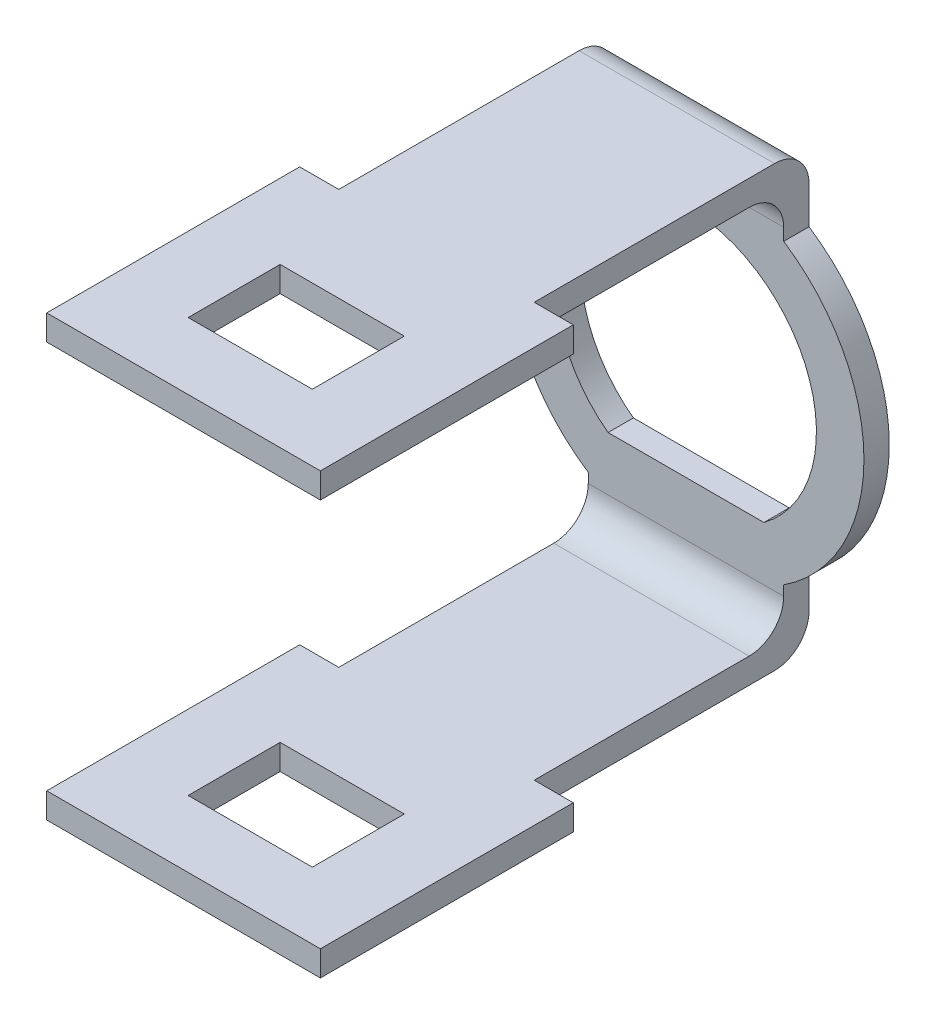
SolidWorks part; units mm, degrees
ref_plane "Front Plane" through (0, 0, 0) normal (0, 0, 1) x (1, 0, 0)
ref_plane "Top Plane" through (0, 0, 0) normal (0, 1, 0) x (1, 0, 0)
ref_plane "Right Plane" through (0, 0, 0) normal (1, 0, 0) x (0, 0, -1)
sketch "Sketch1" plane through (0, 0, 0) normal (0, 0, 1) x (1, 0, 0)
  line L0 (-3.3886, -4.5495) -> (3.3886, -4.5495)
  line L2 (3.952, -6.655) -> (-3.9716, -6.655)
  line L5 (4.25, 6.4687) -> (-4.25, 6.4807)
  arc A0 (3.3886, -4.5495) -> (-3.3886, -4.5495) centre (0, 0) ccw
  arc A2 (-4.25, 6.4807) -> (-3.9716, -6.655) centre (0, 0) ccw
  arc A3 (3.952, -6.655) -> (4.25, 6.4687) centre (0, 0) ccw
extrude "Boss-Extrude1" add sketch "Sketch1" along normal blind 1.1
ref_plane "Plane1" through (0, -8.4, 0) normal (0, -1, 0) x (-1, 0, 0)
sketch "Sketch3" plane through (0, -8.4, 0) normal (0, -1, 0) x (-1, 0, 0)
  line L0 (2.7, -20.05) -> (2.7, -16.05)
  line L1 (-5.95, -22.95) -> (5.95, -22.95)
  line L2 (-2.7, -20.05) -> (-2.7, -16.05)
  line L3 (2.55, -20.05) -> (-2.55, -20.05) construction
  line L4 (-5.95, -22.95) -> (-5.95, -11.95)
  line L5 (-5.95, -11.95) -> (5.95, -11.95)
  line L6 (5.95, -22.95) -> (5.95, -11.95)
  line L7 (-2.7, -16.05) -> (2.7, -16.05)
  line L8 (2.7, -20.05) -> (-2.7, -20.05)
  point P2 (0, -20.95)
extrude "Boss-Extrude2" add sketch "Sketch3" along normal blind 1.1 separate body
ref_plane "Plane2" through (0, 8.5, 0) normal (0, 1, 0) x (1, 0, 0)
sketch "Sketch4" plane through (0, 8.5, 0) normal (0, 1, 0) x (1, 0, 0)
  line L4 (-5.95, -22.95) -> (5.95, -22.95)
  line L5 (-5.95, -11.95) -> (-5.95, -22.95)
  line L6 (5.95, -11.95) -> (-5.95, -11.95)
  line L7 (5.95, -22.95) -> (5.95, -11.95)
  line L8 (-5.95, -22.95) -> (5.95, -22.95)
  line L9 (-5.95, -11.95) -> (-5.95, -22.95)
  line L10 (5.95, -11.95) -> (-5.95, -11.95)
  line L11 (5.95, -22.95) -> (5.95, -11.95)
  line L12 (-2.7, -16.05) -> (-2.7, -20.05)
  line L13 (2.7, -16.05) -> (-2.7, -16.05)
  line L14 (2.7, -20.05) -> (2.7, -16.05)
  line L15 (-2.7, -20.05) -> (2.7, -20.05)
  line L16 (-2.7, -16.05) -> (-2.7, -20.05)
  line L17 (2.7, -16.05) -> (-2.7, -16.05)
  line L18 (2.7, -20.05) -> (2.7, -16.05)
  line L19 (-2.7, -20.05) -> (2.7, -20.05)
  dimension "D1" = 0
  dimension "D2" = 0
extrude "Boss-Extrude3" add sketch "Sketch4" along normal blind 1.1 separate body
sketch "Sketch2" plane through (0, 0, 0) normal (1, 0, 0) x (0, 0, -1)
  line L1 (-1.1, -6.2451) -> (0, -6.2451)
  line L3 (-1.1, 6.2098) -> (0, 6.2098)
  line L4 (-11.95, 9.6) -> (-11.95, 8.5) construction
  line L5 (-11.95, 9.6) -> (-11.95, 8.5)
  line L6 (-11.95, -9.5) -> (-11.95, -8.4) construction
  line L7 (-11.95, -9.5) -> (-11.95, -8.4)
  line L8 (-1.1, 6.2098) -> (-1.1, 7)
  line L9 (-11.95, 8.5) -> (-2.6, 8.5)
  line L10 (-1.1, -6.2451) -> (-1.1, -6.9)
  line L11 (-11.95, -8.4) -> (-2.6, -8.4)
  line L12 (0, 6.2098) -> (0, 8.1)
  line L13 (-11.95, 9.6) -> (-1.5, 9.6)
  line L14 (0, -6.2451) -> (0, -8)
  line L15 (-11.95, -9.5) -> (-1.5, -9.5)
  arc A0 (-2.6, 8.5) -> (-1.1, 7) centre (-2.6, 7) cw
  arc A1 (-2.6, -8.4) -> (-1.1, -6.9) centre (-2.6, -6.9) ccw
  arc A2 (-1.5, -9.5) -> (0, -8) centre (-1.5, -8) ccw
  arc A3 (-1.5, 9.6) -> (0, 8.1) centre (-1.5, 8.1) cw
  dimension "D1" = 1.5
  dimension "D2" = 1.5
  dimension "D3" = 1.5
  dimension "D4" = 1.5
extrude "Boss-Extrude4" add sketch "Sketch2" along normal mid plane 8.5
